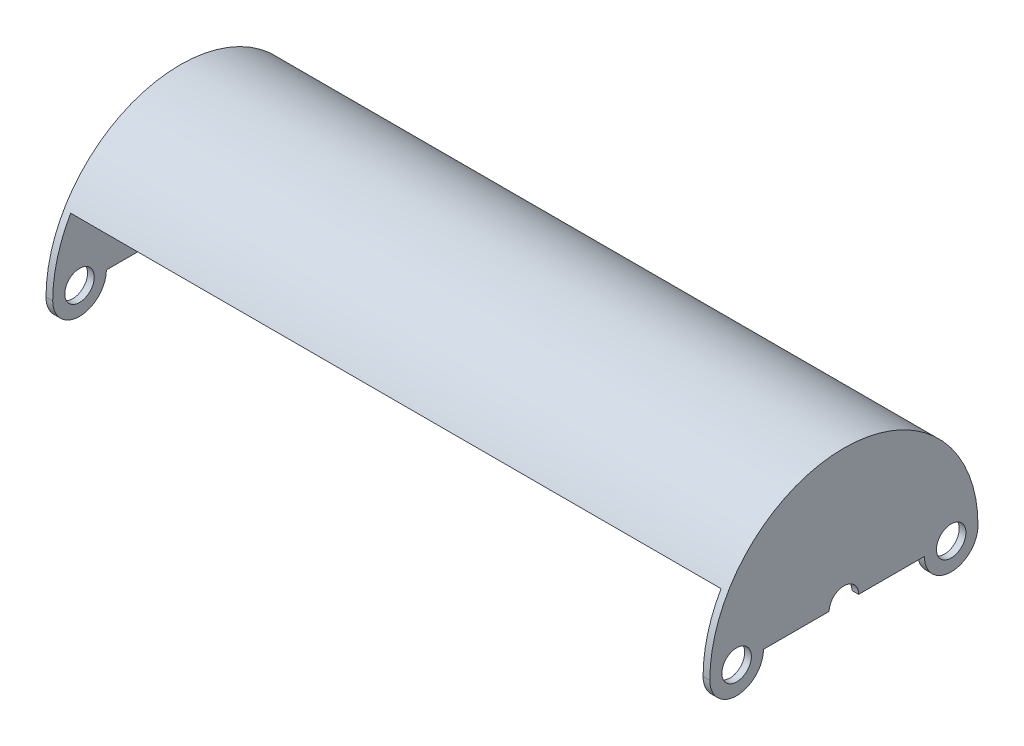
SolidWorks part; units mm, degrees
ref_plane "Front Plane" through (0, 0, 0) normal (0, 0, 1) x (1, 0, 0)
ref_plane "Top Plane" through (0, 0, 0) normal (0, 1, 0) x (1, 0, 0)
ref_plane "Right Plane" through (0, 0, 0) normal (1, 0, 0) x (0, 0, -1)
sketch "Sketch1" plane through (0, 0, 0) normal (1, 0, 0) x (0, 0, -1)
  line L0 (-31.75, 0) -> (-30.1625, 0) construction
  line L1 (30.1625, 0) -> (31.75, 0)
  line L2 (0, 0) -> (-27.4963, 15.875)
  arc A0 (31.75, 0) -> (-31.75, 0) centre (0, 0) ccw
  arc A1 (30.1625, 0) -> (-30.1625, 0) centre (0, 0) ccw
  dimension "D1" = 63.5
  dimension "D2" = 1.5875
  dimension "D3" = 30
extrude "Boss-Extrude1" add sketch "Sketch1" along normal mid plane 153.9875 contours A1 L1 A0 L2
sketch "Sketch2" plane through (76.9938, 0, 0) normal (1, 0, 0) x (0, 0, -1)
  line L0 (-19.05, 0) -> (-3.4925, 0)
  line L1 (3.4925, 0) -> (19.05, 0)
  circle A0 centre (-25.4, 0) radius 3.4925
  arc A1 (31.75, 0) -> (-31.75, 0) centre (0, 0) ccw
  circle A2 centre (25.4, 0) radius 3.4925
  arc A3 (-31.75, 0) -> (-19.05, 0) centre (-25.4, 0) ccw
  arc A4 (19.05, 0) -> (31.75, 0) centre (25.4, 0) ccw
  arc A5 (3.4925, 0) -> (-3.4925, 0) centre (0, 0) ccw
  dimension "D1" = 6.985
  dimension "D3" = 6.985
  dimension "D5" = 12.7
  dimension "D6" = 31.75
  dimension "D2" = 25.4
  dimension "D4" = 25.4
extrude "Boss-Extrude2" add sketch "Sketch2" along normal blind 1.5875
mirror "Mirror1" about plane through (0, 0, 0) normal (1, 0, 0) of "Boss-Extrude2"
